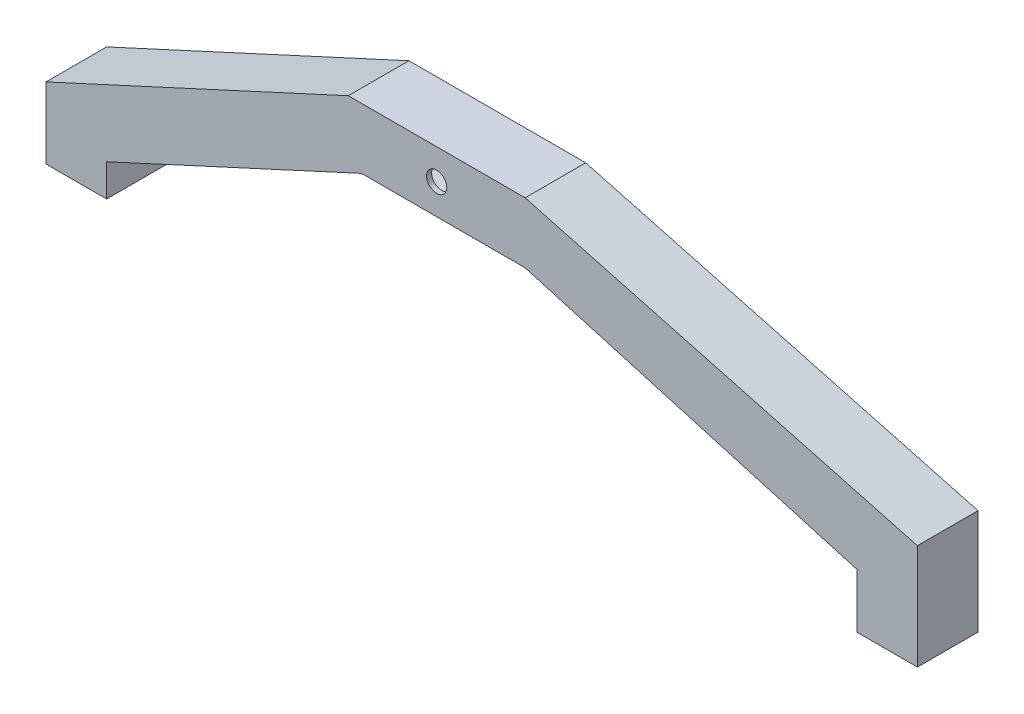
SolidWorks part; units mm, degrees
material "1060 Alloy"
ref_plane "Front Plane" through (0, 0, 0) normal (0, 0, 1) x (1, 0, 0)
ref_plane "Top Plane" through (0, 0, 0) normal (0, 1, 0) x (1, 0, 0)
ref_plane "Right Plane" through (0, 0, 0) normal (1, 0, 0) x (0, 0, -1)
sketch "Sketch1" plane through (0, 0, 0) normal (0, 0, 1) x (1, 0, 0)
  line L0 (-17.5, 6) -> (-77.3429, -21.55)
  line L1 (-17.5, 6) -> (17.5, 6)
  line L3 (-14.8704, -6) -> (17.5, -6)
  line L5 (17.5, 6) -> (95.1571, -14.8129)
  line L6 (-77.3429, -35.63) -> (-65.3429, -35.63)
  line L7 (82.9391, -35.63) -> (95.1571, -35.63)
  line L10 (-77.3429, -35.63) -> (-65.3429, -35.63) construction
  line L11 (-65.3429, -29.2361) -> (-14.8704, -6)
  line L14 (-74.9005, -35.63) -> (-65.3429, -35.63)
  line L17 (-77.3429, -21.55) -> (-77.3429, -35.63)
  line L18 (-77.3429, -35.63) -> (-65.3429, -35.63)
  line L19 (-65.3429, -29.2361) -> (-65.3429, -35.63)
  line L20 (17.5, -6) -> (82.9391, -24.7767)
  line L21 (95.1571, -35.63) -> (82.9391, -35.63)
  line L22 (95.1571, -35.63) -> (95.1571, -14.8129)
  line L24 (82.9391, -35.63) -> (82.9391, -24.7767)
  line L25 (82.9391, -35.63) -> (95.1571, -35.63) construction
  point P0 (0, 0)
  point P13 (0, -35.63)
  dimension "D1" = 35
  dimension "D2" = 12
  dimension "D3" = 65.88
  dimension "D4" = 155.28
  dimension "D6" = 172.5
  dimension "D9" = 163.99
extrude "Boss-Extrude1" add sketch "Sketch1" along normal blind 12 contours L24 L7 L22 L5 L1 L0 L17 L6 L19 L11 L3 L20
shell "Shell1" thickness 1
sketch "Sketch2" plane through (0, -35.63, 0) normal (0, -1, 0) x (1, 0, 0)
  line L0 (95.1571, 12) -> (95.1571, 0) construction
  line L1 (84.1571, 11.1014) -> (94.1571, 11.1014)
  line L2 (84.1571, 11.1014) -> (84.1571, 1.1014)
  line L3 (84.1571, 1.1014) -> (94.1571, 1.1014)
  line L4 (94.1571, 11.1014) -> (94.1571, 1.1014)
  line L5 (84.1571, 11.1014) -> (94.1571, 1.1014) construction
  line L6 (84.1571, 1.1014) -> (94.1571, 11.1014) construction
  point P0 (89.1571, 6.1014)
  dimension "D1" = 10
  dimension "D2" = 10
  dimension "D3" = 1
extrude "Cut-Extrude1" cut sketch "Sketch2" against normal blind 12
sketch "Sketch3" plane through (0, 0, 12) normal (0, 0, 1) x (1, 0, 0)
  line L0 (-17.5, 6) -> (17.5, 6) construction
  circle A0 centre (0, 0) radius 2
  dimension "D1" = 4
  dimension "D2" = 6
  dimension "D3" = 17.5
extrude "Cut-Extrude2" cut sketch "Sketch3" against normal blind 12
sketch "Sketch5" plane through (0, -35.63, 0) normal (0, -1, 0) x (1, 0, 0)
  line L0 (82.9391, 0) -> (83.1571, 0)
  line L1 (82.9391, 12) -> (95.1571, 12)
  line L2 (82.9391, 12) -> (82.9391, 0)
  line L4 (95.1571, 12) -> (95.1571, 0)
  line L5 (95.1571, 12) -> (83.1571, 12)
  line L6 (95.1571, 12) -> (95.1571, 0)
  line L7 (95.1571, 0) -> (83.1571, 0)
  line L8 (83.1571, 12) -> (83.1571, 0)
  line M12 (82.9391, 0) -> (95.1571, 0)
  line M15 (82.9391, 12) -> (82.9391, 0)
  dimension "D1" = 12
  dimension "D2" = 12
extrude "Cut-Extrude3" cut sketch "Sketch5" against normal up to surface (10.8533 mm away) contours L8 L1 M15 M12
